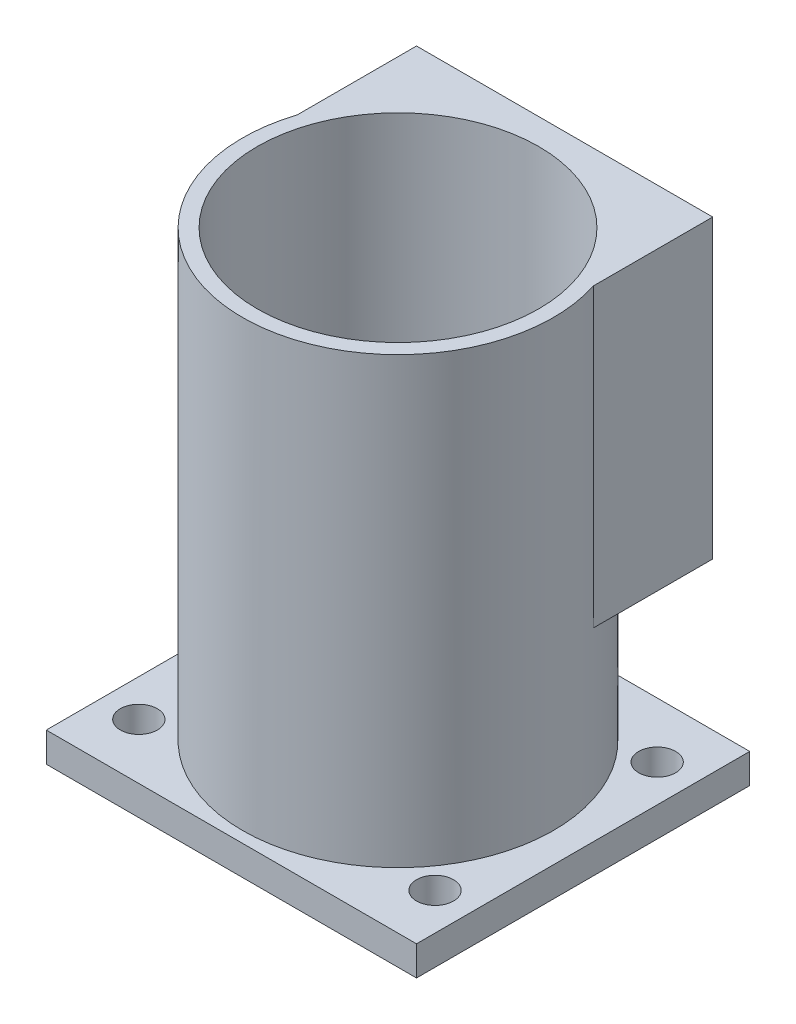
SolidWorks part; units mm, degrees
ref_plane "Front Plane" through (0, 0, 0) normal (0, 0, 1) x (1, 0, 0)
ref_plane "Top Plane" through (0, 0, 0) normal (0, 1, 0) x (1, 0, 0)
ref_plane "Right Plane" through (0, 0, 0) normal (1, 0, 0) x (0, 0, -1)
sketch "Sketch1" plane through (0, 0, 0) normal (0, 1, 0) x (1, 0, 0)
  line L0 (0, -9.525) -> (6.35, -9.525) construction
  line L1 (0, 0) -> (63.5, 0)
  line L2 (0, 0) -> (0, -57.15)
  line L3 (0, -57.15) -> (63.5, -57.15)
  line L4 (63.5, 0) -> (63.5, -57.15)
  line L5 (57.15, -9.525) -> (63.5, -9.525) construction
  line L6 (0, -28.575) -> (63.5, -28.575) construction
  circle A0 centre (6.35, -9.525) radius 3.175
  circle A1 centre (57.15, -9.525) radius 3.175
  circle A4 centre (57.15, -47.625) radius 3.175
  circle A5 centre (6.35, -47.625) radius 3.175
  dimension "D3" = 50.8
  dimension "D4" = 6.35
  dimension "D1" = 63.5
  dimension "D2" = 57.15
  dimension "D5" = 9.525
extrude "Boss-Extrude1" add sketch "Sketch1" along normal blind 5.08
sketch "Sketch2" plane through (0, 5.08, 0) normal (0, 1, 0) x (1, 0, 0)
  line L0 (31.75, 0) -> (31.75, -57.15) construction
  line L1 (63.5, 0) -> (0, 0) construction
  line L2 (0, -57.15) -> (63.5, -57.15) construction
  line L3 (0, -28.575) -> (63.5, -28.575) construction
  line L4 (0, 0) -> (0, -57.15) construction
  line L5 (63.5, -57.15) -> (63.5, 0) construction
  circle A0 centre (31.75, -28.575) radius 24.13
  circle A1 centre (31.75, -28.575) radius 26.67
extrude "Boss-Extrude2" add sketch "Sketch2" along normal blind 76.2 contours A1 | A0
sketch "Sketch4" plane through (0, 0, 0) normal (0, 0, -1) x (-1, 0, 0)
  line L7 (-31.75, 81.28) -> (-31.75, 0) construction
  line L8 (-5.08, 81.28) -> (-58.42, 81.28) construction
  line L9 (-63.5, 0) -> (0, 0) construction
  line L11 (-57.15, 81.28) -> (-6.35, 81.28)
  line L12 (-57.15, 81.28) -> (-57.15, 30.48)
  line L13 (-57.15, 30.48) -> (-6.35, 30.48)
  line L14 (-6.35, 81.28) -> (-6.35, 30.48)
  dimension "D1" = 50.8
  dimension "D2" = 50.8
extrude "Boss-Extrude3" add sketch "Sketch4" against normal up to surface (20.443 mm away)
